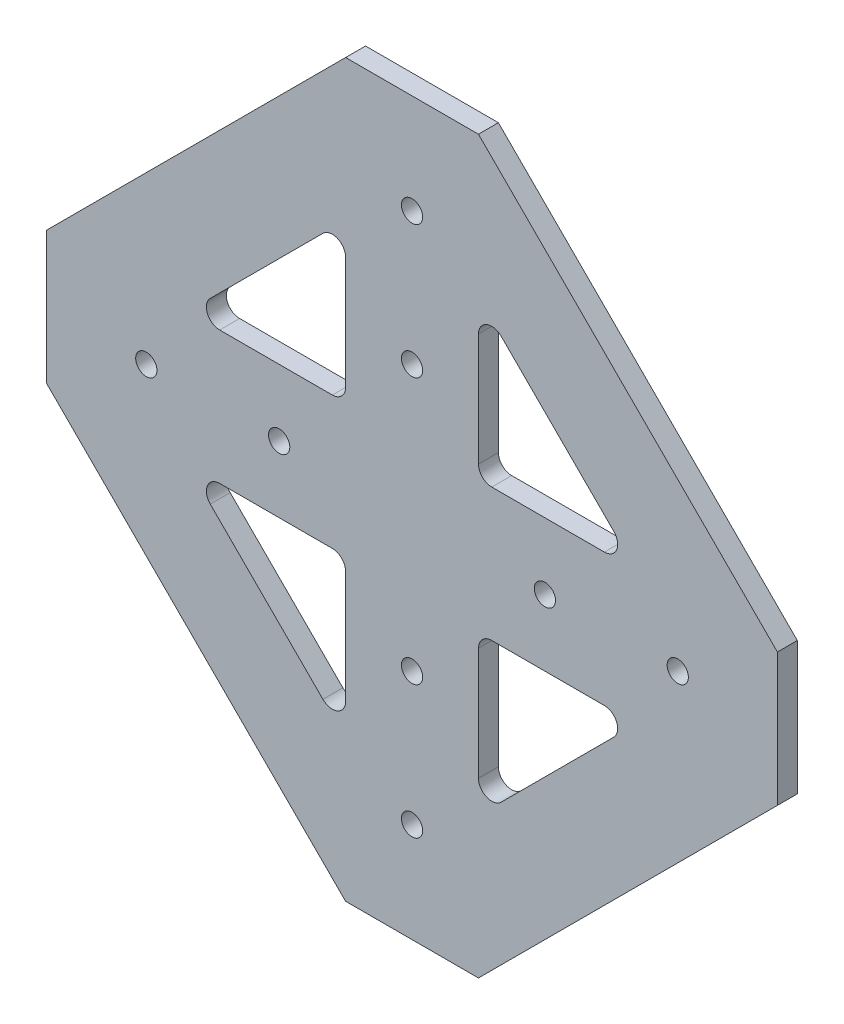
SolidWorks part; units mm, degrees
material "Thornel Mat VMA"
ref_plane "Front Plane" through (0, 0, 0) normal (0, 0, 1) x (1, 0, 0)
ref_plane "Top Plane" through (0, 0, 0) normal (0, 1, 0) x (1, 0, 0)
ref_plane "Right Plane" through (0, 0, 0) normal (1, 0, 0) x (0, 0, -1)
sketch "Sketch1" plane through (0, 0, 0) normal (0, 0, 1) x (1, 0, 0)
  line L1 (-253.4899, 347.497) -> (-233.4899, 347.497)
  line L2 (-298.4899, 302.497) -> (-298.4899, 282.497)
  line L3 (-253.4899, 237.497) -> (-233.4899, 237.497)
  line L4 (-188.4899, 302.497) -> (-188.4899, 282.497)
  line L7 (-412.5912, 347.497) -> (-233.4899, 347.497) construction
  line L8 (-233.4899, 237.497) -> (-412.5912, 237.497) construction
  line L10 (-233.4899, 302.497) -> (-233.4899, 592.497) construction
  line L11 (-298.4899, 302.497) -> (-253.4899, 347.497)
  line L12 (-233.4899, 347.497) -> (-188.4899, 302.497)
  line L13 (-233.4899, 237.497) -> (-188.4899, 282.497)
  line L14 (-298.4899, 282.497) -> (-253.4899, 237.497)
  point P0 (-298.4899, 347.497)
  point P1 (-188.4899, 237.497)
  point P2 (-298.4899, 237.497)
  point P3 (-188.4899, 347.497)
  point P4 (-283.4899, 347.497)
  point P7 (-283.4899, 267.497)
  point P8 (-285.2211, 237.497)
  point P11 (-201.9561, 347.497)
  dimension "D1" = 45
extrude "Extrude1" add sketch "Sketch1" along normal blind 3
sketch "Sketch2" plane through (0, 0, 3) normal (0, 0, 1) x (1, 0, 0)
  circle A0 centre (-203.4899, 292.497) radius 1.6 construction
  circle A1 centre (-223.4899, 292.497) radius 1.6 construction
  circle A2 centre (-243.4899, 252.497) radius 1.6 construction
  circle A3 centre (-243.4899, 272.497) radius 1.6 construction
  circle A4 centre (-283.4899, 292.497) radius 1.6 construction
  circle A5 centre (-263.4899, 292.497) radius 1.6 construction
  circle A6 centre (-243.4899, 312.497) radius 1.6 construction
  circle A7 centre (-243.4899, 332.497) radius 1.6 construction
  circle A8 centre (-203.4899, 292.497) radius 1.6
  circle A9 centre (-223.4899, 292.497) radius 1.6
  circle A10 centre (-243.4899, 252.497) radius 1.6
  circle A11 centre (-243.4899, 272.497) radius 1.6
  circle A12 centre (-283.4899, 292.497) radius 1.6
  circle A13 centre (-263.4899, 292.497) radius 1.6
  circle A14 centre (-243.4899, 312.497) radius 1.6
  circle A15 centre (-243.4899, 332.497) radius 1.6
extrude "Cut-Extrude1" cut sketch "Sketch2" against normal blind 3
sketch "Sketch3" plane through (0, 0, 3) normal (0, 0, 1) x (1, 0, 0)
  line L0 (-243.4899, 347.497) -> (-243.4899, 292.497) construction
  line L1 (-233.4899, 347.497) -> (-253.4899, 347.497) construction
  line L2 (-243.4899, 292.497) -> (-298.4899, 292.497) construction
  line L3 (-298.4899, 302.497) -> (-298.4899, 282.497) construction
  line L4 (-256.9041, 322.8696) -> (-273.8625, 305.9113)
  line L5 (-272.4483, 302.497) -> (-255.4899, 302.497)
  line L6 (-253.4899, 304.497) -> (-253.4899, 321.4554)
  line L7 (-253.4899, 347.497) -> (-298.4899, 302.497) construction
  line L8 (-233.4899, 304.497) -> (-233.4899, 321.4554)
  line L9 (-214.5316, 302.497) -> (-231.4899, 302.497)
  line L10 (-230.0757, 322.8696) -> (-213.1173, 305.9113)
  line L11 (-230.0757, 262.1245) -> (-213.1173, 279.0828)
  line L12 (-214.5316, 282.497) -> (-231.4899, 282.497)
  line L13 (-233.4899, 280.497) -> (-233.4899, 263.5387)
  line L14 (-253.4899, 280.497) -> (-253.4899, 263.5387)
  line L15 (-272.4483, 282.497) -> (-255.4899, 282.497)
  line L16 (-256.9041, 262.1245) -> (-273.8625, 279.0828)
  arc A0 (-255.4899, 302.497) -> (-253.4899, 304.497) centre (-255.4899, 304.497) ccw
  arc A1 (-256.9041, 322.8696) -> (-253.4899, 321.4554) centre (-255.4899, 321.4554) cw
  arc A2 (-273.8625, 305.9113) -> (-272.4483, 302.497) centre (-272.4483, 304.497) ccw
  arc A3 (-213.1173, 305.9113) -> (-214.5316, 302.497) centre (-214.5316, 304.497) cw
  arc A4 (-230.0757, 322.8696) -> (-233.4899, 321.4554) centre (-231.4899, 321.4554) ccw
  arc A5 (-231.4899, 302.497) -> (-233.4899, 304.497) centre (-231.4899, 304.497) cw
  arc A6 (-231.4899, 282.497) -> (-233.4899, 280.497) centre (-231.4899, 280.497) ccw
  arc A7 (-230.0757, 262.1245) -> (-233.4899, 263.5387) centre (-231.4899, 263.5387) cw
  arc A8 (-213.1173, 279.0828) -> (-214.5316, 282.497) centre (-214.5316, 280.497) ccw
  arc A9 (-273.8625, 279.0828) -> (-272.4483, 282.497) centre (-272.4483, 280.497) cw
  arc A10 (-256.9041, 262.1245) -> (-253.4899, 263.5387) centre (-255.4899, 263.5387) ccw
  arc A11 (-255.4899, 282.497) -> (-253.4899, 280.497) centre (-255.4899, 280.497) cw
  dimension "D4" = 2
  dimension "D1" = 10
  dimension "D2" = 10
  dimension "D3" = 15
extrude "Extrude2" cut sketch "Sketch3" against normal blind 10
